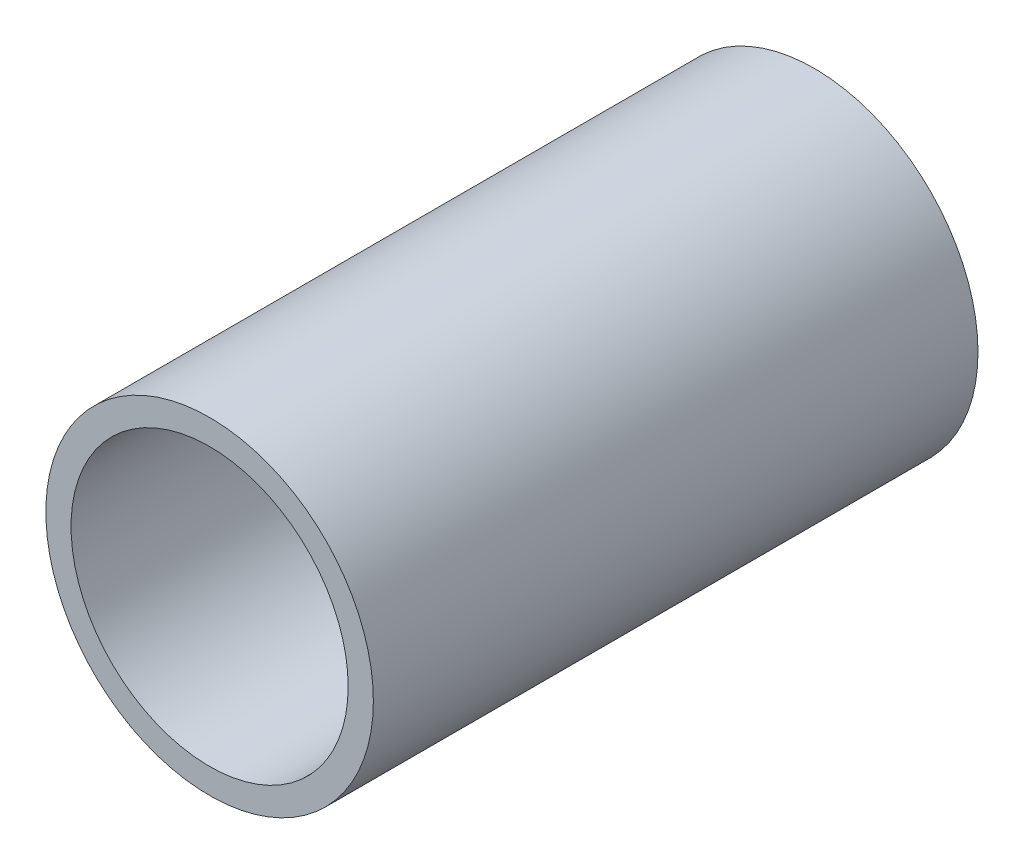
SolidWorks part; units mm, degrees
ref_plane "Front Plane" through (0, 0, 0) normal (0, 0, 1) x (1, 0, 0)
ref_plane "Top Plane" through (0, 0, 0) normal (0, 1, 0) x (1, 0, 0)
ref_plane "Right Plane" through (0, 0, 0) normal (1, 0, 0) x (0, 0, -1)
sketch "Sketch1" plane through (0, 0, 0) normal (0, 0, 1) x (1, 0, 0)
  circle A0 centre (0, 0) radius 3.25
  dimension "D1" = 6.5
extrude "Boss-Extrude1" add sketch "Sketch1" along normal blind 12
sketch "Sketch4" plane through (0, 0, 12) normal (0, 0, 1) x (1, 0, 0)
  circle A0 centre (0, 0) radius 2.75
  dimension "D1" = 5.5
extrude "Cut-Extrude3" cut sketch "Sketch4" against normal blind 12
